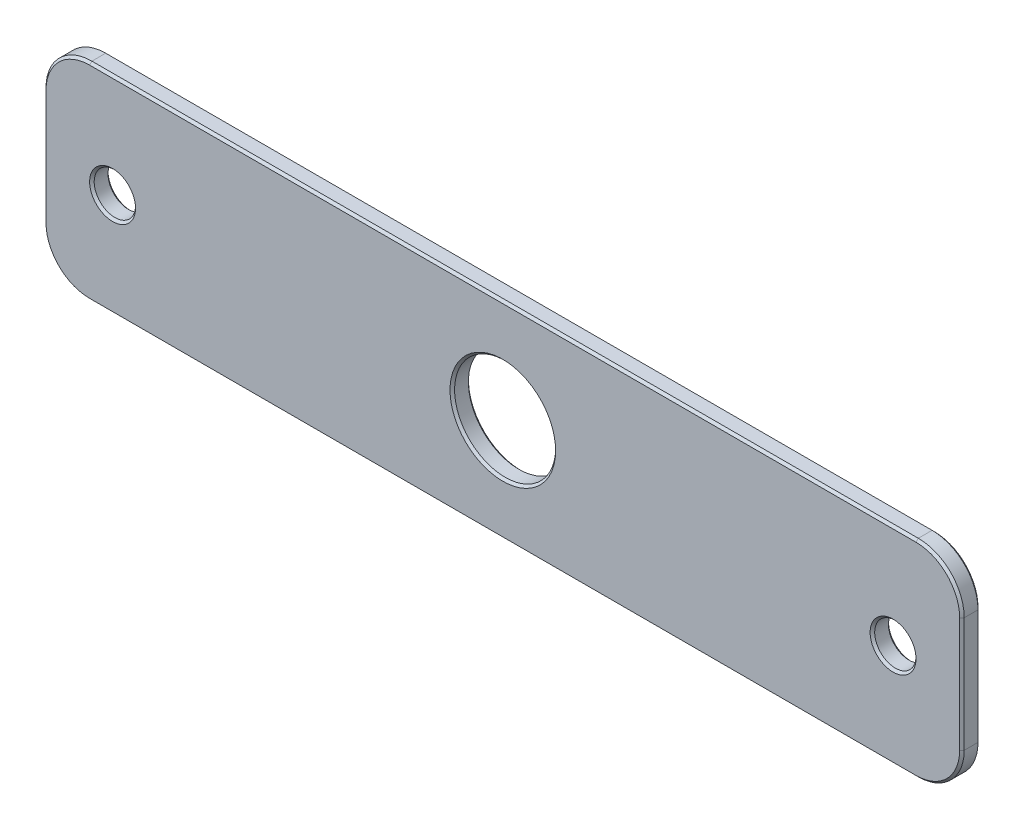
SolidWorks part; units mm, degrees
ref_plane "Plan de face" through (0, 0, 0) normal (0, 0, 1) x (1, 0, 0)
ref_plane "Plan de dessus" through (0, 0, 0) normal (0, 1, 0) x (1, 0, 0)
ref_plane "Plan de droite" through (0, 0, 0) normal (1, 0, 0) x (0, 0, -1)
sketch "Esquisse1" plane through (0, 0, 0) normal (0, 0, 1) x (1, 0, 0)
  line L1 (-121.919, 81.5789) -> (78.081, 81.5789)
  line L2 (-121.919, 81.5789) -> (-121.919, 36.5789)
  line L3 (-121.919, 36.5789) -> (78.081, 36.5789)
  line L4 (78.081, 81.5789) -> (78.081, 36.5789)
  dimension "D1" = 200
  dimension "D2" = 45
extrude "Boss.-Extru.1" add sketch "Esquisse1" along normal blind 4
fillet "Congé2" radius 10 4 edges at (-121.919, 81.5789, 2) (-121.919, 36.5789, 2) (78.081, 36.5789, 2) (78.081, 81.5789, 2)
hole_wizard "Dégagement M81" positions "Esquisse2" profile "Esquisse3" hole size "M8" standard "Ansi Metric" end condition through all
sketch "Esquisse2" plane through (0, 0, 4) normal (0, 0, 1) x (1, 0, 0)
  line L0 (68.081, 81.5789) -> (-111.919, 81.5789) construction
  line L1 (-121.919, 71.5789) -> (-121.919, 46.5789) construction
  line L2 (78.081, 46.5789) -> (78.081, 71.5789) construction
  point P0 (-106.919, 59.0789)
  point P2 (63.081, 59.0789)
  dimension "D1" = 22.5
  dimension "D2" = 22.5
  dimension "D3" = 15
  dimension "D4" = 15
sketch "Esquisse3" plane through (-106.919, 59.0789, 4) normal (1, 0, 0) x (0, -1, 0)
  line L0 (0, 0) -> (0, 4)
  line L1 (0, 4) -> (4.5, 4)
  line L2 (4.5, 4) -> (4.5, 0)
  line L5 (4.5, 0) -> (0, 0)
  line L11 (0, -6.35) -> (0, 107.95) construction
  dimension "Diamètre du perçage jusqu'au prochain" = 9
  dimension "Profondeur du perçage jusqu'au prochain" = 4
hole_wizard "Dégagement M201" positions "Esquisse4" profile "Esquisse5" hole size "M20" standard "Ansi Metric" end condition through all
sketch "Esquisse4" plane through (0, 0, 4) normal (0, 0, 1) x (1, 0, 0)
  line L0 (78.081, 46.5789) -> (78.081, 71.5789) construction
  line L1 (-111.919, 36.5789) -> (68.081, 36.5789) construction
  point P0 (-21.919, 59.0789)
  point P9 (-19.6628, 39.1025)
  point P10 (0, 0)
  dimension "D1" = 100
  dimension "D2" = 22.5
sketch "Esquisse5" plane through (-21.919, 59.0789, 4) normal (1, 0, 0) x (0, -1, 0)
  line L0 (0, 0) -> (0, 4)
  line L1 (0, 4) -> (11, 4)
  line L2 (11, 4) -> (11, 0)
  line L5 (11, 0) -> (0, 0)
  line L11 (0, -6.35) -> (0, 107.95) construction
  dimension "Diamètre du perçage jusqu'au prochain" = 22
  dimension "Profondeur du perçage jusqu'au prochain" = 4
chamfer "Chanfrein2" distance 0.5 angle 45 16 edges at (-21.919, 81.5789, 4) (-121.919, 59.0789, 4) (78.081, 59.0789, 4) (-21.919, 36.5789, 4) (78.081, 59.0789, 0) (-21.919, 81.5789, 0) (-121.919, 59.0789, 0) (-21.919, 36.5789, 0) (-118.9901, 78.65, 4) (75.1521, 78.65, 4) (-118.9901, 39.5079, 4) (75.1521, 39.5079, 4) (-118.9901, 78.65, 0) (75.1521, 78.65, 0) (-118.9901, 39.5079, 0) (75.1521, 39.5079, 0)
chamfer "Chanfrein3" distance 0.5 angle 45 6 edges at (-102.419, 59.0789, 4) (-102.419, 59.0789, 0) (-10.919, 59.0789, 4) (-10.919, 59.0789, 0) (67.581, 59.0789, 4) (67.581, 59.0789, 0)
